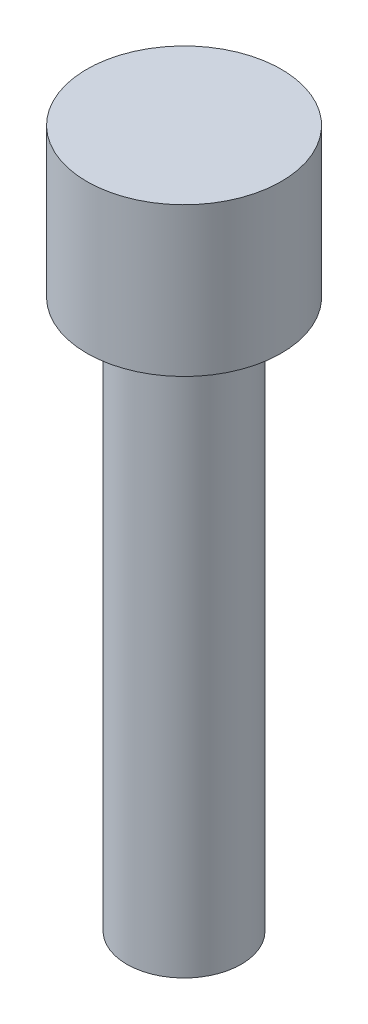
SolidWorks part; units mm, degrees
ref_plane "Front Plane" through (0, 0, 0) normal (0, 0, 1) x (1, 0, 0)
ref_plane "Top Plane" through (0, 0, 0) normal (0, 1, 0) x (1, 0, 0)
ref_plane "Right Plane" through (0, 0, 0) normal (1, 0, 0) x (0, 0, -1)
sketch "Sketch1" plane through (0, 0, 0) normal (0, 1, 0) x (1, 0, 0)
  circle A0 centre (0, 0) radius 2.5
  dimension "D1" = 5
extrude "Boss-Extrude1" add sketch "Sketch1" along normal blind 24
sketch "Sketch2" plane through (0, 24, 0) normal (0, 1, 0) x (1, 0, 0)
  circle A0 centre (0, 0) radius 4.25
  dimension "D1" = 8.5
extrude "Boss-Extrude2" add sketch "Sketch2" along normal blind 6.5
